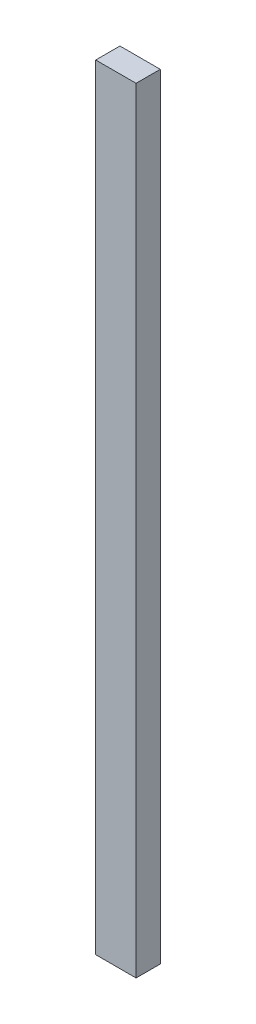
SolidWorks part; units mm, degrees
ref_plane "Front Plane" through (0, 0, 0) normal (0, 0, 1) x (1, 0, 0)
ref_plane "Top Plane" through (0, 0, 0) normal (0, 1, 0) x (1, 0, 0)
ref_plane "Right Plane" through (0, 0, 0) normal (1, 0, 0) x (0, 0, -1)
sketch "Sketch1" plane through (0, 0, 0) normal (0, 1, 0) x (1, 0, 0)
  line L1 (0, 0) -> (63.5, 0)
  line L2 (0, 0) -> (0, -38.1)
  line L3 (0, -38.1) -> (63.5, -38.1)
  line L4 (63.5, 0) -> (63.5, -38.1)
  dimension "D1" = 38.1
  dimension "D2" = 63.5
extrude "Boss-Extrude1" add sketch "Sketch1" along normal blind 1219.2
